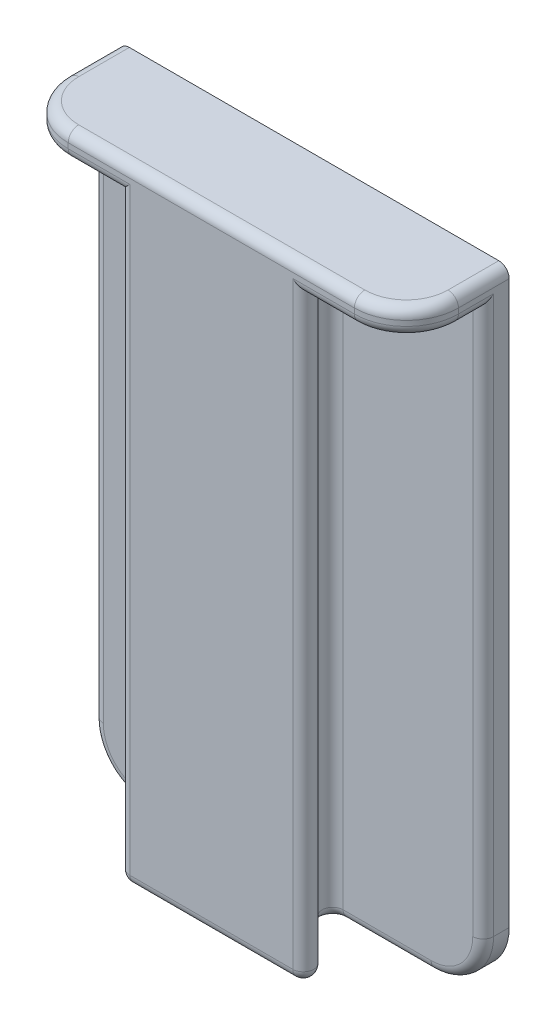
SolidWorks part; units mm, degrees
ref_plane "Front" through (0, 0, 0) normal (0, 0, 1) x (1, 0, 0)
ref_plane "Top" through (0, 0, 0) normal (0, 1, 0) x (1, 0, 0)
ref_plane "Right" through (0, 0, 0) normal (1, 0, 0) x (0, 0, -1)
sketch "Sketch1" plane through (0, 0, 0) normal (0, 0, 1) x (1, 0, 0)
  line L1 (-37.5, 57.5) -> (37.5, 57.5)
  line L2 (-37.5, 57.5) -> (-37.5, -57.5)
  line L3 (-37.5, -57.5) -> (37.5, -57.5)
  line L4 (37.5, 57.5) -> (37.5, -57.5)
  line L5 (-37.5, 57.5) -> (37.5, -57.5) construction
  line L6 (-37.5, -57.5) -> (37.5, 57.5) construction
  point P0 (0, 0)
  dimension "D1" = 75
  dimension "D2" = 115
extrude "Boss-Extrude1" add sketch "Sketch1" along normal blind 5
sketch "Sketch4" plane through (0, 57.5, 0) normal (0, 1, 0) x (1, 0, 0)
  line L0 (0, 0) -> (0, -29.3627) construction
  line L1 (-5.75, -5) -> (5.75, -5)
  line L2 (37.5, -5) -> (-37.5, -5) construction
  line L3 (5.75, -5) -> (20.5, -19.75)
  line L4 (20.5, -19.75) -> (-20.5, -19.75)
  line L5 (-5.75, -5) -> (-20.5, -19.75)
  point P9 (0, -5)
  point P11 (0, -19.75)
  dimension "D1" = 45
  dimension "D2" = 14.75
  dimension "D3" = 5.75
extrude "Boss-Extrude2" add sketch "Sketch4" against normal up to surface (115 mm away) up to face at (0, -57.5, 2.5)
fillet "Fillet1" radius 2 4 edges at (-5.75, 0, 5) (5.75, 0, 5) (20.5, 0, 19.75) (-20.5, 0, 19.75)
sketch "Sketch5" plane through (0, 57.5, 0) normal (0, 1, 0) x (1, 0, 0)
  line L0 (-15.6716, -19.75) -> (15.6716, -19.75) construction
  line L1 (-37.5, 0) -> (37.5, 0)
  line L2 (-37.5, 0) -> (-37.5, -19.75)
  line L3 (-37.5, -19.75) -> (37.5, -19.75)
  line L4 (37.5, 0) -> (37.5, -19.75)
extrude "Boss-Extrude3" add sketch "Sketch5" along normal blind 5
fillet "Fillet2" radius 10 4 edges at (-37.5, 60, 19.75) (37.5, 60, 19.75) (37.5, -57.5, 2.5) (-37.5, -57.5, 2.5)
fillet "Fillet3" radius 2 24 edges at (-37.5, 62.5, 4.875) (-34.5711, 62.5, 16.8211) (0, 62.5, 19.75) (34.5711, 62.5, 16.8211) (-37.5, 57.5, 7.375) (-34.5711, 57.5, 16.8211) (37.5, 57.5, 7.375) (21.5858, 57.5, 19.75) (37.5, 5, 5) (34.5711, -54.5711, 5) (19.0392, -57.5, 5) (8.7307, -57.5, 6.2346) (13.125, -57.5, 12.375) (17.5193, -57.5, 18.5154) (-37.5, 5, 5) (-34.5711, -54.5711, 5) (-19.0392, -57.5, 5) (-8.7307, -57.5, 6.2346) (-13.125, -57.5, 12.375) (-17.5193, -57.5, 18.5154) (37.5, 62.5, 4.875) (-21.5858, 57.5, 19.75) (34.5711, 57.5, 16.8211) (0, -57.5, 19.75)
